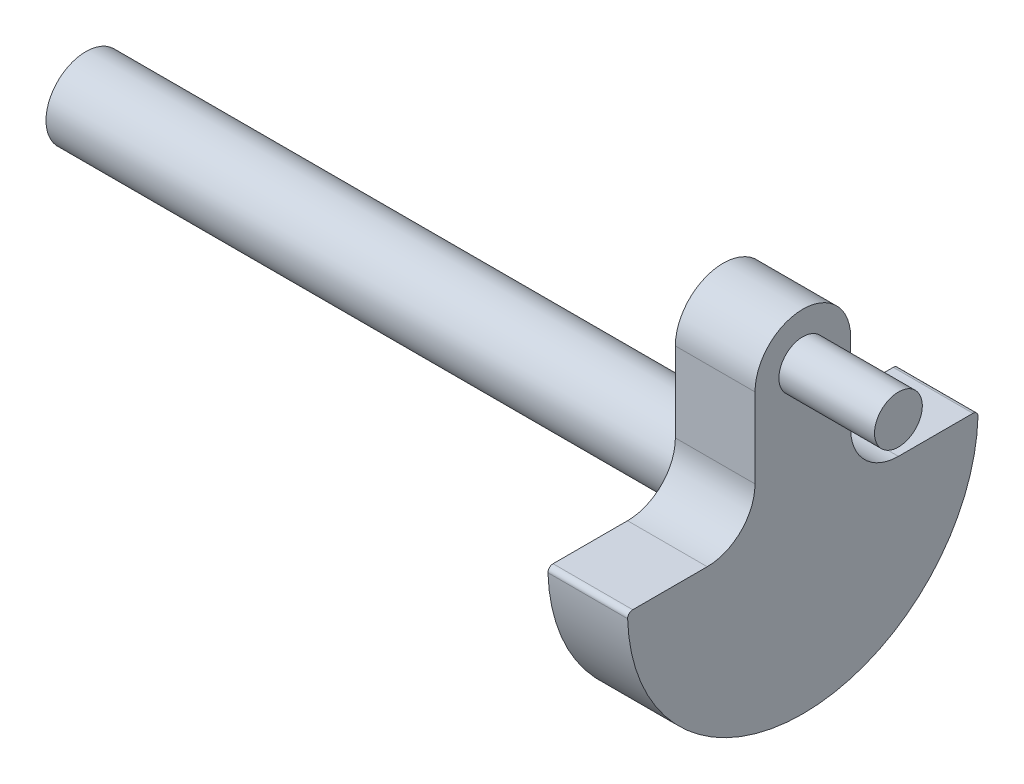
SolidWorks part; units mm, degrees
material "Cast Carbon Steel"
ref_plane "Front Plane" through (0, 0, 0) normal (0, 0, 1) x (1, 0, 0)
ref_plane "Top Plane" through (0, 0, 0) normal (0, 1, 0) x (1, 0, 0)
ref_plane "Right Plane" through (0, 0, 0) normal (1, 0, 0) x (0, 0, -1)
sketch "Sketch2" plane through (0, 0, 0) normal (1, 0, 0) x (0, 0, -1)
  line L0 (8.7312, 0) -> (2.3813, 0)
  line L1 (-2.3813, 6.35) -> (-2.3812, 0)
  line L2 (2.3813, 6.35) -> (2.3813, 0)
  line L3 (-2.3812, 0) -> (-8.7312, 0)
  circle A0 centre (0, 6.35) radius 1.1906
  circle A1 centre (0, 0) radius 1.9844
  arc A2 (-8.7312, 0) -> (8.7312, 0) centre (0, 0) ccw
  arc A3 (2.3813, 6.35) -> (-2.3813, 6.35) centre (0, 6.35) ccw
  point P13 (0, 0)
  dimension "D1" = 2.3813
  dimension "D2" = 3.9688
  dimension "D3" = 17.4625
  dimension "D4" = 4.7625
  dimension "D5" = 6.35
extrude "Boss-Extrude1" add sketch "Sketch2" along normal blind 3.9688
sketch "Sketch3" plane through (0, 0, 0) normal (-1, 0, 0) x (0, 0, 1)
  circle A0 centre (0, 6.35) radius 1.1906 construction
  circle A1 centre (0, 6.35) radius 1.1906
extrude "Boss-Extrude2" add sketch "Sketch3" against normal blind 8.7312
sketch "Sketch4" plane through (0, 0, 0) normal (-1, 0, 0) x (0, 0, 1)
  circle A0 centre (0, 0) radius 1.9844
  dimension "D1" = 3.9688
extrude "Boss-Extrude3" add sketch "Sketch4" along normal blind 31.75 separate body
sketch "Sketch5" plane through (0, 0, 0) normal (1, 0, 0) x (0, 0, -1)
  circle A0 centre (0, 0) radius 1.9844 construction
  circle A1 centre (0, 0) radius 1.9844
extrude "Boss-Extrude4" add sketch "Sketch5" along normal blind 3.9688
fillet "Fillet2" radius 2.3813 2 edges at (1.9844, 0, -2.3813) (1.9844, 0, 2.3812)
fillet "Fillet3" radius 0.254 2 edges at (1.9844, 0, -8.7312) (1.9844, 0, 8.7312)
